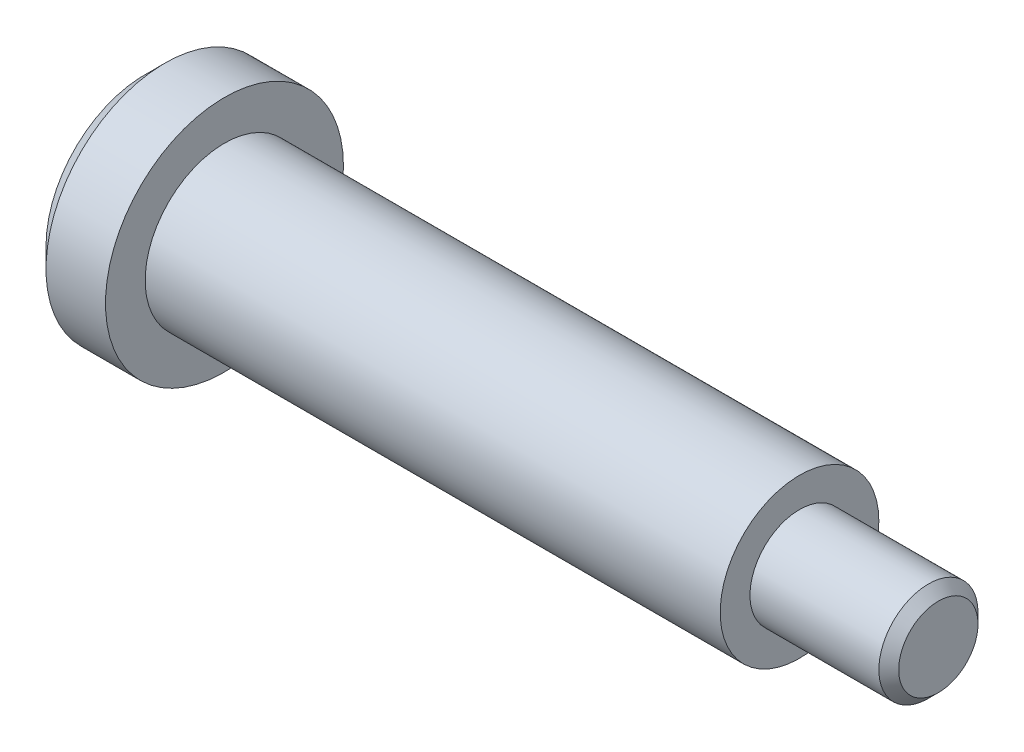
SolidWorks part; units mm, degrees
ref_plane "Front Plane" through (0, 0, 0) normal (0, 0, 1) x (1, 0, 0)
ref_plane "Top Plane" through (0, 0, 0) normal (0, 1, 0) x (1, 0, 0)
ref_plane "Right Plane" through (0, 0, 0) normal (1, 0, 0) x (0, 0, -1)
sketch "Sketch1" plane through (0, 0, 0) normal (1, 0, 0) x (0, 0, -1)
  circle A0 centre (0, 0) radius 6
  dimension "D1" = 12
extrude "Boss-Extrude1" add sketch "Sketch1" along normal blind 4
sketch "Sketch2" plane through (4, 0, 0) normal (1, 0, 0) x (0, 0, -1)
  circle A0 centre (0, 0) radius 4
  dimension "D1" = 8
extrude "Boss-Extrude2" add sketch "Sketch2" along normal blind 29
sketch "Sketch3" plane through (33, 0, 0) normal (1, 0, 0) x (0, 0, -1)
  circle A0 centre (0, 0) radius 2.5
  dimension "D1" = 5
extrude "Boss-Extrude3" add sketch "Sketch3" along normal blind 7
chamfer "Chamfer1" distance 0.5 angle 45 1 edges at (40, 0, -2.5)
chamfer "Chamfer2" distance 1 angle 45 1 edges at (0, 0, -6)
sketch "Sketch4" plane through (0, 0, 0) normal (-1, 0, 0) x (0, 0, 1)
  circle A0 centre (0, 0) radius 2.5
  dimension "D1" = 5
extrude "Cut-Extrude1" cut sketch "Sketch4" against normal blind 1
fillet "Fillet1" radius 0.5 1 edges at (0, 0, 2.5)
scale "Scale1" scale about origin uniform scaling yes scale factor 0.5
